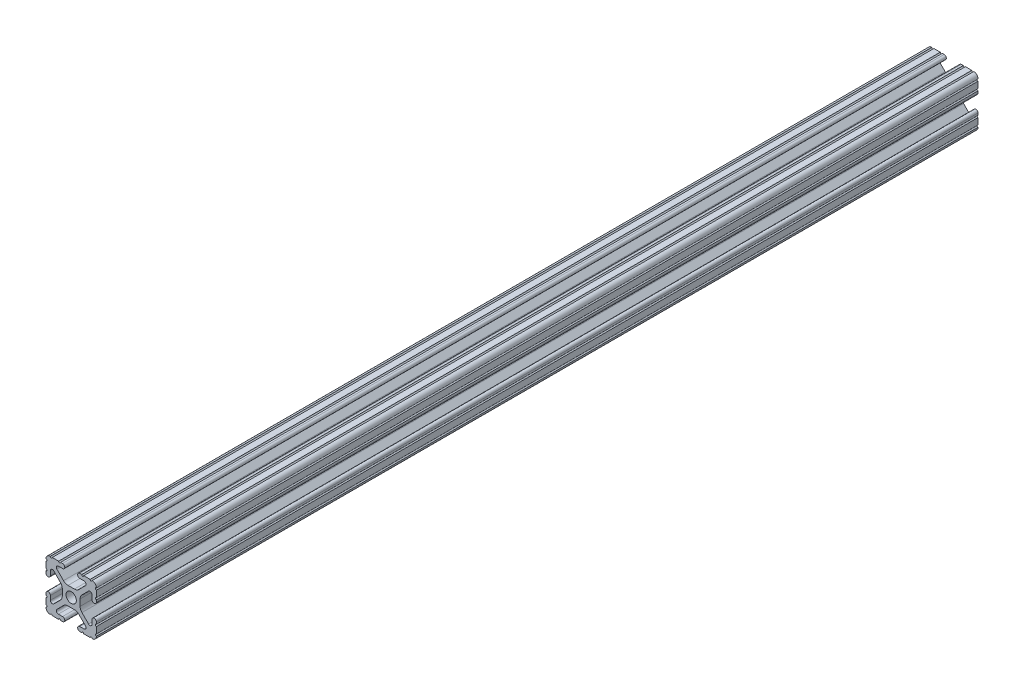
SolidWorks part; units mm, degrees
ref_plane "Front Plane" through (0, 0, 0) normal (0, 0, 1) x (1, 0, 0)
ref_plane "Top Plane" through (0, 0, 0) normal (0, 1, 0) x (1, 0, 0)
ref_plane "Right Plane" through (0, 0, 0) normal (1, 0, 0) x (0, 0, -1)
ref_plane "Plane1" through (0, 0, 0) normal (0, 0, 1) x (1, 0, 0)
sketch "Sketch1" plane through (0, 0, 0) normal (0, 0, 1) x (1, 0, 0)
  line L0 (-12.7, 9.5504) -> (-12.7, 6.3331)
  line L1 (-12.7, 5.3171) -> (-12.7, 4.3434)
  line L2 (-10.4902, 4.3434) -> (-10.4902, 6.4748)
  line L3 (-8.7558, 7.1932) -> (-5.4257, 3.8632)
  line L4 (-4.4958, 1.6181) -> (-4.4958, -1.6181)
  line L5 (-5.4257, -3.8632) -> (-8.7558, -7.1932)
  line L6 (-10.4902, -6.4748) -> (-10.4902, -4.3434)
  line L7 (-12.7, -4.3434) -> (-12.7, -5.3171)
  line L8 (-12.7, -6.3331) -> (-12.7, -9.5504)
  line L9 (-9.5504, -12.7) -> (-6.3331, -12.7)
  line L10 (-5.3171, -12.7) -> (-4.3434, -12.7)
  line L11 (-4.3434, -10.4902) -> (-6.4748, -10.4902)
  line L12 (-7.1932, -8.7558) -> (-3.8632, -5.4257)
  line L13 (-1.6181, -4.4958) -> (1.6181, -4.4958)
  line L14 (3.8632, -5.4257) -> (7.1932, -8.7558)
  line L15 (6.4748, -10.4902) -> (4.3434, -10.4902)
  line L16 (4.3434, -12.7) -> (5.3171, -12.7)
  line L17 (6.3331, -12.7) -> (9.5504, -12.7)
  line L18 (12.7, -9.5504) -> (12.7, -6.3331)
  line L19 (12.7, -5.3171) -> (12.7, -4.3434)
  line L20 (10.4902, -4.3434) -> (10.4902, -6.4748)
  line L21 (8.7558, -7.1932) -> (5.4257, -3.8632)
  line L22 (4.4958, -1.6181) -> (4.4958, 1.6181)
  line L23 (5.4257, 3.8632) -> (8.7558, 7.1932)
  line L24 (10.4902, 6.4748) -> (10.4902, 4.3434)
  line L25 (12.7, 4.3434) -> (12.7, 5.3171)
  line L26 (12.7, 6.3331) -> (12.7, 9.5504)
  line L27 (9.5504, 12.7) -> (6.3331, 12.7)
  line L28 (5.3171, 12.7) -> (4.3434, 12.7)
  line L29 (4.3434, 10.4902) -> (6.4748, 10.4902)
  line L30 (7.1932, 8.7558) -> (3.8632, 5.4257)
  line L31 (1.6181, 4.4958) -> (-1.6181, 4.4958)
  line L32 (-3.8632, 5.4257) -> (-7.1932, 8.7558)
  line L33 (-6.4748, 10.4902) -> (-4.3434, 10.4902)
  line L34 (-4.3434, 12.7) -> (-5.3171, 12.7)
  line L35 (-6.3331, 12.7) -> (-9.5504, 12.7)
  arc A0 (-12.7, 6.3331) -> (-12.7, 5.3171) centre (-12.7, 5.8251) cw
  arc A1 (-12.7, 4.3434) -> (-10.4902, 4.3434) centre (-11.5951, 4.3434) ccw
  arc A2 (-10.4902, 6.4748) -> (-8.7558, 7.1932) centre (-9.4742, 6.4748) cw
  arc A3 (-5.4257, 3.8632) -> (-4.4958, 1.6181) centre (-7.6708, 1.6181) cw
  arc A4 (-4.4958, -1.6181) -> (-5.4257, -3.8632) centre (-7.6708, -1.6181) cw
  arc A5 (-8.7558, -7.1932) -> (-10.4902, -6.4748) centre (-9.4742, -6.4748) cw
  arc A6 (-10.4902, -4.3434) -> (-12.7, -4.3434) centre (-11.5951, -4.3434) ccw
  arc A7 (-12.7, -5.3171) -> (-12.7, -6.3331) centre (-12.7, -5.8251) cw
  arc A8 (-12.7, -9.5504) -> (-12.6998, -10.5664) centre (-12.7, -10.0584) cw
  arc A9 (-12.6998, -10.5664) -> (-10.5664, -12.6998) centre (-10.5918, -10.5918) ccw
  arc A10 (-10.5664, -12.6998) -> (-9.5504, -12.7) centre (-10.0584, -12.7) cw
  arc A11 (-6.3331, -12.7) -> (-5.3171, -12.7) centre (-5.8251, -12.7) cw
  arc A12 (-4.3434, -12.7) -> (-4.3434, -10.4902) centre (-4.3434, -11.5951) ccw
  arc A13 (-6.4748, -10.4902) -> (-7.1932, -8.7558) centre (-6.4748, -9.4742) cw
  arc A14 (-3.8632, -5.4257) -> (-1.6181, -4.4958) centre (-1.6181, -7.6708) cw
  arc A15 (1.6181, -4.4958) -> (3.8632, -5.4257) centre (1.6181, -7.6708) cw
  arc A16 (7.1932, -8.7558) -> (6.4748, -10.4902) centre (6.4748, -9.4742) cw
  arc A17 (4.3434, -10.4902) -> (4.3434, -12.7) centre (4.3434, -11.5951) ccw
  arc A18 (5.3171, -12.7) -> (6.3331, -12.7) centre (5.8251, -12.7) cw
  arc A19 (9.5504, -12.7) -> (10.5664, -12.6998) centre (10.0584, -12.7) cw
  arc A20 (10.5664, -12.6998) -> (12.6998, -10.5664) centre (10.5918, -10.5918) ccw
  arc A21 (12.6998, -10.5664) -> (12.7, -9.5504) centre (12.7, -10.0584) cw
  arc A22 (12.7, -6.3331) -> (12.7, -5.3171) centre (12.7, -5.8251) cw
  arc A23 (12.7, -4.3434) -> (10.4902, -4.3434) centre (11.5951, -4.3434) ccw
  arc A24 (10.4902, -6.4748) -> (8.7558, -7.1932) centre (9.4742, -6.4748) cw
  arc A25 (5.4257, -3.8632) -> (4.4958, -1.6181) centre (7.6708, -1.6181) cw
  arc A26 (4.4958, 1.6181) -> (5.4257, 3.8632) centre (7.6708, 1.6181) cw
  arc A27 (8.7558, 7.1932) -> (10.4902, 6.4748) centre (9.4742, 6.4748) cw
  arc A28 (10.4902, 4.3434) -> (12.7, 4.3434) centre (11.5951, 4.3434) ccw
  arc A29 (12.7, 5.3171) -> (12.7, 6.3331) centre (12.7, 5.8251) cw
  arc A30 (12.7, 9.5504) -> (12.6998, 10.5664) centre (12.7, 10.0584) cw
  arc A31 (12.6998, 10.5664) -> (10.5664, 12.6998) centre (10.5918, 10.5918) ccw
  arc A32 (10.5664, 12.6998) -> (9.5504, 12.7) centre (10.0584, 12.7) cw
  arc A33 (6.3331, 12.7) -> (5.3171, 12.7) centre (5.8251, 12.7) cw
  arc A34 (4.3434, 12.7) -> (4.3434, 10.4902) centre (4.3434, 11.5951) ccw
  arc A35 (6.4748, 10.4902) -> (7.1932, 8.7558) centre (6.4748, 9.4742) cw
  arc A36 (3.8632, 5.4257) -> (1.6181, 4.4958) centre (1.6181, 7.6708) cw
  arc A37 (-1.6181, 4.4958) -> (-3.8632, 5.4257) centre (-1.6181, 7.6708) cw
  arc A38 (-7.1932, 8.7558) -> (-6.4748, 10.4902) centre (-6.4748, 9.4742) cw
  arc A39 (-4.3434, 10.4902) -> (-4.3434, 12.7) centre (-4.3434, 11.5951) ccw
  arc A40 (-5.3171, 12.7) -> (-6.3331, 12.7) centre (-5.8251, 12.7) cw
  arc A41 (-9.5504, 12.7) -> (-10.5664, 12.6998) centre (-10.0584, 12.7) cw
  arc A42 (-10.5664, 12.6998) -> (-12.6998, 10.5664) centre (-10.5918, 10.5918) ccw
  arc A43 (-12.6998, 10.5664) -> (-12.7, 9.5504) centre (-12.7, 10.0584) cw
  circle A44 centre (0, 0) radius 2.6035
extrude "Boss-Extrude1" add sketch "Sketch1" against normal blind 444.5
